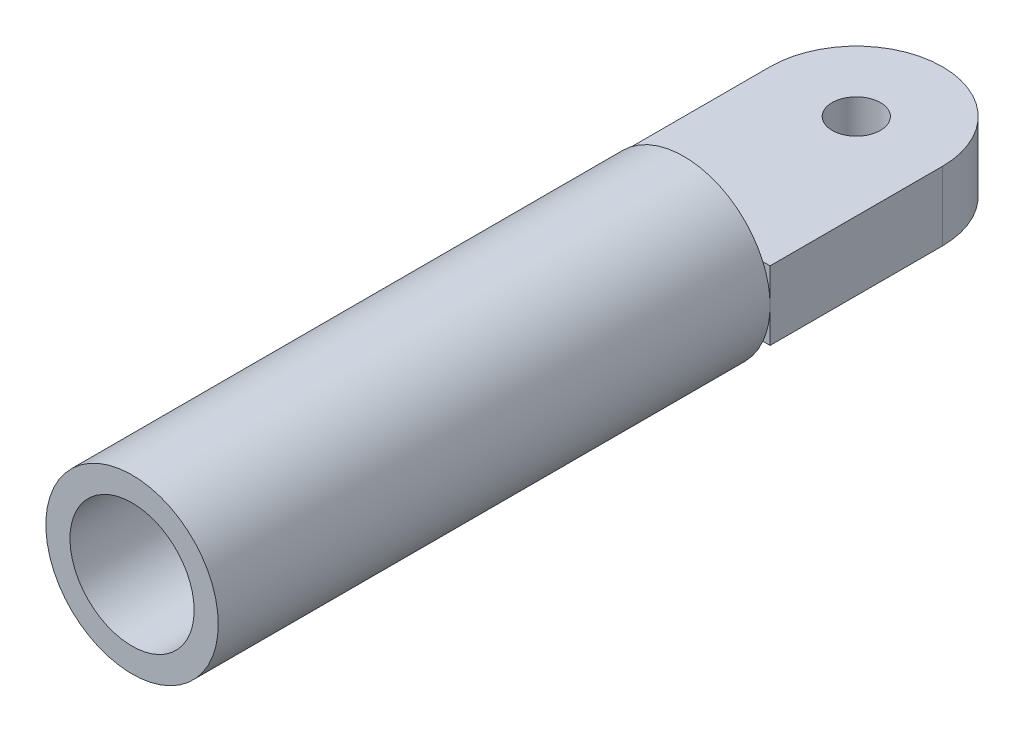
SolidWorks part; units mm, degrees
ref_plane "Front Plane" through (0, 0, 0) normal (0, 0, 1) x (1, 0, 0)
ref_plane "Top Plane" through (0, 0, 0) normal (0, 1, 0) x (1, 0, 0)
ref_plane "Right Plane" through (0, 0, 0) normal (1, 0, 0) x (0, 0, -1)
sketch "Sketch1" plane through (0, 0, 0) normal (0, 0, 1) x (1, 0, 0)
  circle A0 centre (0, 0) radius 12.5
  circle A1 centre (0, 0) radius 9
  dimension "D1" = 25
  dimension "D2" = 18
extrude "Boss-Extrude1" add sketch "Sketch1" along normal blind 80
sketch "Sketch2" plane through (0, 0, 0) normal (0, 1, 0) x (1, 0, 0)
  line L1 (-12.5, 0) -> (12.5, 0)
  line L2 (-12.5, 0) -> (-12.5, 25)
  line L4 (12.5, 0) -> (12.5, 25)
  arc A0 (-12.5, 25) -> (12.5, 25) centre (0, 25) cw
  circle A3 centre (0, 25) radius 3.5
  dimension "D1" = 12.5
  dimension "D3" = 7
  dimension "D2" = 25
  dimension "D4" = 25
extrude "Boss-Extrude2" add sketch "Sketch2" along normal mid plane 10
